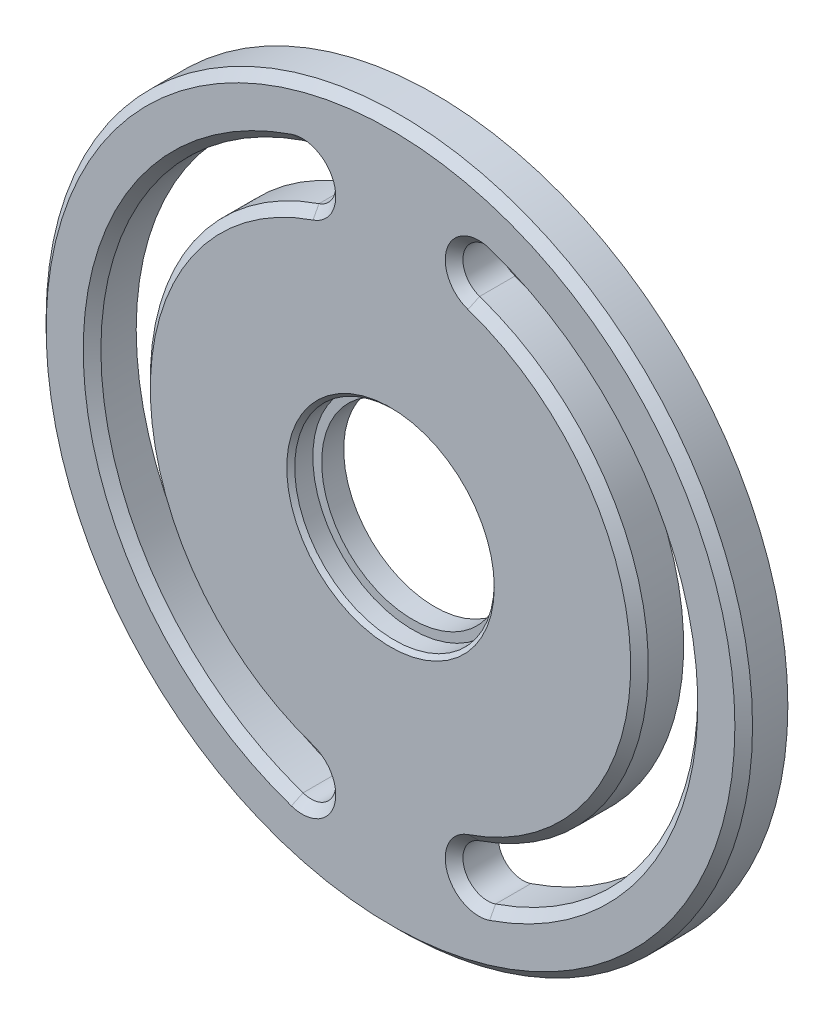
SolidWorks part; units mm, degrees
ref_plane "Front Plane" through (0, 0, 0) normal (0, 0, 1) x (1, 0, 0)
ref_plane "Top Plane" through (0, 0, 0) normal (0, 1, 0) x (1, 0, 0)
ref_plane "Right Plane" through (0, 0, 0) normal (1, 0, 0) x (0, 0, -1)
sketch "Sketch1" plane through (0, 0, 0) normal (0, 0, 1) x (1, 0, 0)
  line L0 (-39.37, 0) -> (39.37, 0) construction
  line L1 (0, 50.8) -> (0, -50.8) construction
  circle A0 centre (0, 0) radius 50.8
  arc A1 (-12.7, 37.2654) -> (-12.7, -37.2654) centre (0, 0) ccw construction
  arc A2 (-13.8471, 40.6313) -> (-13.8471, -40.6313) centre (0, 0) ccw
  arc A3 (-11.5529, 33.8995) -> (-11.5529, -33.8995) centre (0, 0) ccw
  arc A4 (-11.5529, 33.8995) -> (-13.8471, 40.6313) centre (-12.7, 37.2654) ccw
  arc A5 (-13.8471, -40.6313) -> (-11.5529, -33.8995) centre (-12.7, -37.2654) ccw
  arc A6 (12.7, 37.2654) -> (12.7, -37.2654) centre (0, 0) cw construction
  arc A7 (13.8471, 40.6313) -> (13.8471, -40.6313) centre (0, 0) cw
  arc A8 (11.5529, 33.8995) -> (11.5529, -33.8995) centre (0, 0) cw
  arc A9 (11.5529, 33.8995) -> (13.8471, 40.6313) centre (12.7, 37.2654) cw
  arc A10 (13.8471, -40.6313) -> (11.5529, -33.8995) centre (12.7, -37.2654) cw
  point P5 (-39.37, 0)
  point P15 (0, 0)
  point P18 (39.37, 0)
  dimension "D1" = 101.6
  dimension "D2" = 3.556
  dimension "D4" = 39.37
  dimension "D3" = 25.4
extrude "Boss-Extrude1" add sketch "Sketch1" along normal blind 6.35
chamfer "Chamfer1" distance 1.27 angle 45 9 edges at (50.8, 0, 6.35) (-9.3341, -38.4125, 6.35) (-35.814, 0, 6.35) (-9.3341, 38.4125, 6.35) (-42.926, 0, 6.35) (9.3341, -38.4125, 6.35) (42.926, 0, 6.35) (9.3341, 38.4125, 6.35) (35.814, 0, 6.35)
hole_wizard "CBORE for 1/2 Heavy Hex Bolt1" positions "Sketch4" profile "Sketch5" counterbore size "1/2" standard "ANSI Inch" end condition through all
sketch "Sketch4" plane through (0, 0, 6.35) normal (0, 0, 1) x (1, 0, 0)
  point P0 (0, 0)
sketch "Sketch5" plane through (0, 0, 6.35) normal (1, 0, 0) x (0, -1, 0)
  line L0 (0, 0) -> (0, 6.35)
  line L1 (0, 6.35) -> (13.081, 6.35)
  line L3 (13.081, 6.35) -> (13.081, 3.175)
  line L4 (14.351, 3.175) -> (13.081, 3.175)
  line L5 (14.351, 3.175) -> (14.351, 0.5715)
  line L6 (14.351, 0.5715) -> (14.9225, 0)
  line L7 (14.9225, 0) -> (0, 0)
  line L8 (-14.351, 0.5715) -> (-14.9225, 0) construction
  line L11 (0, -6.35) -> (0, 107.95) construction
  dimension "Thru Hole Dia." = 26.162
  dimension "Thru Hole Depth" = 6.35
  dimension "C'Bore Dia." = 28.702
  dimension "C'Bore Depth" = 3.175
  dimension "Near C'Sink Dia." = 29.845
  dimension "Near C'Sink Angle" = 90
